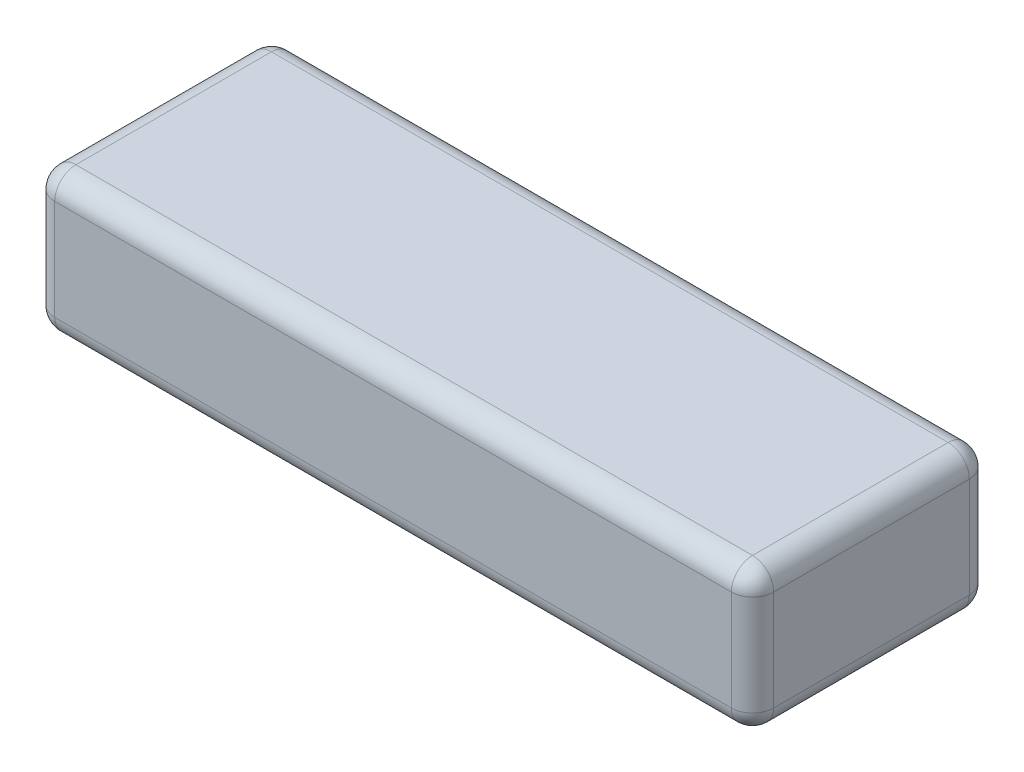
SolidWorks part; units mm, degrees
ref_plane "Alzado" through (0, 0, 0) normal (0, 0, 1) x (1, 0, 0)
ref_plane "Planta" through (0, 0, 0) normal (0, 1, 0) x (1, 0, 0)
ref_plane "Vista lateral" through (0, 0, 0) normal (1, 0, 0) x (0, 0, -1)
sketch "Croquis1" plane through (0, 0, 0) normal (0, 1, 0) x (1, 0, 0)
  line L1 (-68, -22.5) -> (68, -22.5)
  line L2 (-68, -22.5) -> (-68, 22.5)
  line L3 (-68, 22.5) -> (68, 22.5)
  line L4 (68, -22.5) -> (68, 22.5)
  line L5 (-68, -22.5) -> (68, 22.5) construction
  line L6 (-68, 22.5) -> (68, -22.5) construction
  point P0 (0, 0)
extrude "Saliente-Extruir1" add sketch "Croquis1" along normal blind 27
fillet "Redondeo1" radius 4 12 edges at (-68, 13.5, -22.5) (-68, 13.5, 22.5) (68, 13.5, 22.5) (68, 13.5, -22.5) (0, 0, -22.5) (-68, 0, 0) (0, 0, 22.5) (68, 0, 0) (0, 27, 22.5) (-68, 27, 0) (0, 27, -22.5) (68, 27, 0)
